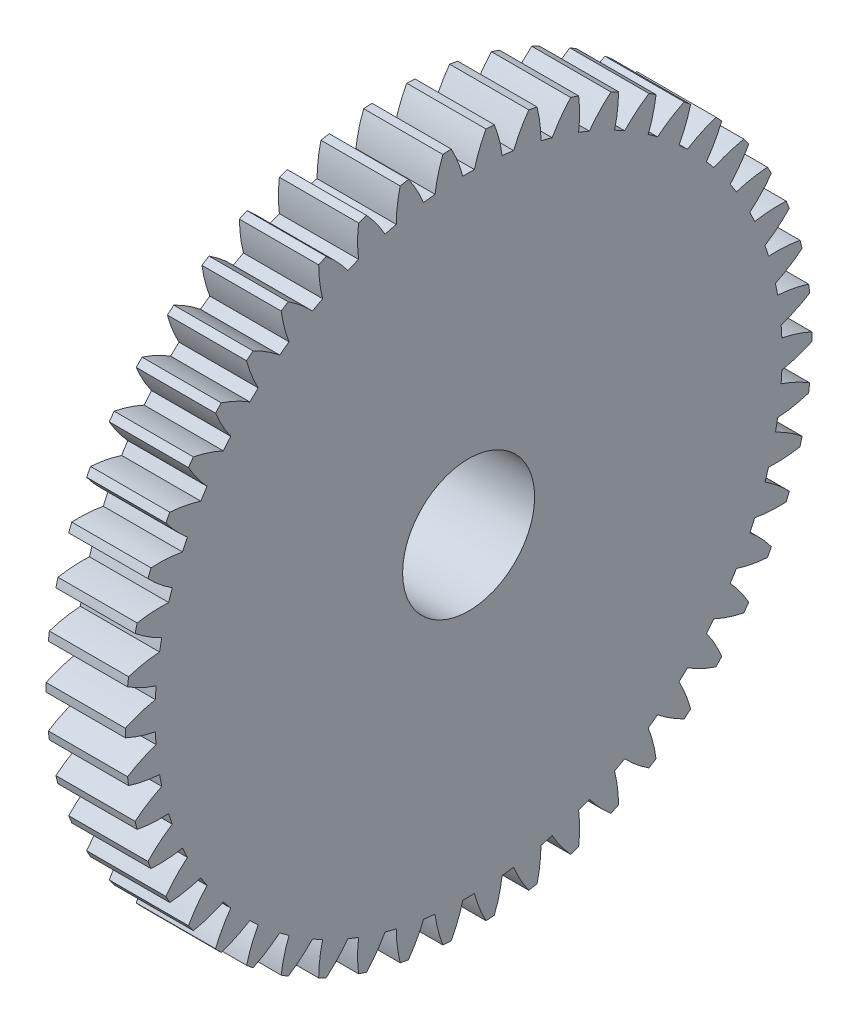
SolidWorks part; units mm, degrees
material "铬红铜，UNS C18200"
ref_plane "Plane1" through (0, 0, 0) normal (0, 0, 1) x (1, 0, 0)
ref_plane "Plane2" through (0, 0, 0) normal (0, 1, 0) x (1, 0, 0)
ref_plane "Plane3" through (0, 0, 0) normal (1, 0, 0) x (0, 0, -1)
sketch "HoldingSke" plane through (0, 0, 0) normal (0, 1, 0) x (1, 0, 0)
  line L0 (0, 0) -> (1.2856, -1.5321)
  line L1 (-15, 0) -> (100, 0) construction
  line L2 (0, 0) -> (-2.1039, 2.3779)
  line L3 (0, 0) -> (-11.863, 4.5341)
  line L4 (0, 0) -> (5.5511, 6.6156)
  line L5 (0, 0) -> (-7.4956, -2.7956)
  line L6 (0, 0) -> (-2.4869, -1.6779)
  line L7 (-2.1039, 2.3779) -> (-0.3819, 10.1904)
  line L8 (-76.2, 54.61) -> (-75.3, 54.61)
  line L9 (-71.009, 38.7566) -> (-53.1078, 45.2721)
  line L10 (-76.2, 71.12) -> (104.1128, 71.12)
  line L11 (0, 0) -> (-3, 0)
  line L12 (-76.2, 101.6) -> (-76.181, 101.6)
  line L13 (24.9733, 27.94) -> (52.9518, 28.4284)
  line L14 (24.9733, 27.94) -> (24.9743, 27.94)
  line L15 (24.9733, 27.94) -> (100.4006, 29.5858)
  line L16 (-63.627, -0.5) -> (-12.827, -0.5)
  circle A0 centre (0, 0) radius 2.5
  circle A1 centre (0, 0) radius 4.5
  circle A2 centre (0, 0) radius 4.5
  circle A3 centre (0, 0) radius 2.5
  dimension "MHD" = 9
  dimension "Hub_dia" = 9
  dimension "Bore" = 5
  dimension "MBD" = 5
  dimension "Num_teeth" = 50
  dimension "Pitch_radius" = 180.3128
  dimension "Pitch" = 2
  dimension "Width" = 3
  dimension "Overall_len" = 8
  dimension "Show_teeth" = 50
  dimension "Thickness" = 3
  dimension "OAL" = 8.0001
  dimension "T_dim" = 0.9
  dimension "Ap" = 20
  dimension "H" = 19.05
  dimension "Backlash" = 0.019
  dimension "Addendum_fac" = 1
  dimension "Dedendum_fac" = 1.25
  dimension "Clearance_fac" = 0.25
  dimension "Dedendum_add" = 0.001
  dimension "Module" = 0.5
sketch "BasProSke" plane through (0, 0, 0) normal (0, 1, 0) x (1, 0, 0)
  line L0 (-10, 0) -> (60, 0) construction
  line L1 (0, 0) -> (0, 13)
  line L2 (0, 0) -> (3, 0)
  line L3 (3, 0) -> (3, 13)
  line L4 (3, 13) -> (0, 13)
  dimension "Diameter" = 26
  dimension "Thickness" = 3
revolve "Base-Revolve" add sketch "BasProSke" angle 360 about L0
sketch "TooCutSke" plane through (0, 0, 0) normal (1, 0, 0) x (0, 0, -1)
  line L1 (0, 0) -> (0, 107) construction
  line L2 (0, 0) -> (-0.4259, 12.4927) construction
  line L3 (0, 0) -> (-1.5691, 24.9404) construction
  line L4 (-0.4259, 12.4927) -> (-0.7846, 12.4702) construction
  arc A0 (0.2187, 11.872) -> (-0.2187, 11.872) centre (0, 0) ccw
  arc A1 (0.6715, 13.0081) -> (-0.6715, 13.0081) centre (0, 0) ccw
  circle A2 centre (0, 0) radius 12.5 construction
  circle A3 centre (0, 0) radius 11.7462 construction
  arc A4 (-0.2187, 11.872) -> (-0.6715, 13.0081) centre (-5.0549, 10.6028) ccw
  arc A5 (0.6715, 13.0081) -> (0.2187, 11.872) centre (5.0549, 10.6028) ccw
  dimension "Root_dia" = 23.748
  dimension "Overcut_dia" = 26.0508
  dimension "Pitch_dia" = 25
  dimension "Base_dia" = 23.4923
  dimension "Flank_rad" = 5
  dimension "Half_ang" = 3.6
  dimension "Half_CT" = 0.3594
extrude "ToothCut" cut sketch "TooCutSke" along normal through all
fillet "Breaks" [suppressed] radius 0.01
fillet "RootFillets" [suppressed] radius 0.126
pattern_circular "TeethCuts" count 50 every 7.2 about axis through (-10, 0, 0) along (1, 0, 0) of "ToothCut", "RootFillets", "Breaks"
sketch "HubNeaOneSke" plane through (0, 0, 0) normal (-1, 0, 0) x (0, 0, 1)
  circle A0 centre (0, 0) radius 4.5
  dimension "Diameter" = 9
extrude "HubNearOne" add sketch "HubNeaOneSke" along normal blind 5.0001
sketch "HubNeaBotSke" plane through (0, 0, 0) normal (-1, 0, 0) x (0, 0, 1)
  circle A0 centre (0, 0) radius 4.5
  dimension "Diameter" = 9
extrude "HubNearBoth" [suppressed] add sketch "HubNeaBotSke" along normal blind 2.5
ref_plane "FarPln" through (3, 0, 0) normal (1, 0, 0) x (0, 0, -1)
sketch "HubFarSke" plane through (3, 0, 0) normal (1, 0, 0) x (0, 0, -1)
  circle A0 centre (0, 0) radius 4.5
  dimension "Diameter" = 9
extrude "HubFar" [suppressed] add sketch "HubFarSke" along normal blind 2.5
sketch "BorSke" plane through (0, 0, 0) normal (1, 0, 0) x (0, 0, -1)
  circle A0 centre (0, 0) radius 2.5
  dimension "Diameter" = 5
extrude "Bore" cut sketch "BorSke" along normal mid plane 16.0001
sketch "KeySke" plane through (0, 0, 0) normal (1, 0, 0) x (0, 0, -1)
  line L0 (-1, 0) -> (-1, 3.4)
  line L1 (-1, 3.4) -> (1, 3.4)
  line L2 (1, 3.4) -> (1, 0)
  line L3 (0, 0) -> (0, 34) construction
  line L4 (-1, 0) -> (1, 0)
  dimension "Offset" = 3.4
  dimension "Width" = 2
extrude "Keyway" [suppressed] cut sketch "KeySke" along normal mid plane 16.0001
pattern_circular "Keyway2" [suppressed] count 2 every 90 about axis through (-10, 0, 0) along (1, 0, 0)
equation "' \"Module@HoldingSke\" = 6.35"
equation "' \"Num_teeth@HoldingSke\" = 12"
equation "' \"Ap@HoldingSke\" =  20"
equation "' \"Width@HoldingSke\" = 0.5 * 25.4"
equation "' \"Hub_dia@HoldingSke\"= 1 * 25.4"
equation "' \"Overall_len@HoldingSke\" = 1.0 * 25.4"
equation "' \"Bore@HoldingSke\" = 0.75 * 25.4"
equation "' \"T_dim@HoldingSke\" = 0.1 * 25.4"
equation "' \"Width@KeySke\" = 0.25 * 25.4"
equation "' \"Show_teeth@HoldingSke\" = 13"
equation "' \"Backlash@HoldingSke\" = 0.009 * 25.4"
equation "' \"Addendum_fac@HoldingSke\" = 1.0"
equation "' \"Dedendum_fac@HoldingSke\" = 1.25"
equation "' \"Dedendum_add@HoldingSke\" = 0.00005 * 25.4"
equation "' \"Clearance_fac@HoldingSke\" = 0.25"
equation "\"Pitch@HoldingSke\" = 1 / \"Module@HoldingSke\""
equation "\"Overcut_dia@TooCutSke\" = (\"Num_teeth@HoldingSke\" + 2 * \"Addendum_fac@HoldingSke\") / \"Pitch@HoldingSke\" + 0.002 * 25.4"
equation "\"Pitch_dia@TooCutSke\" = \"Num_teeth@HoldingSke\" / \"Pitch@HoldingSke\""
equation "\"Base_dia@TooCutSke\" = \"Num_teeth@HoldingSke\" / \"Pitch@HoldingSke\" * cos((\"Ap@HoldingSke\"  * 3.14159265 / 180))"
equation "\"Root_dia@TooCutSke\" = (\"Num_teeth@HoldingSke\" + 2) / \"Pitch@HoldingSke\" - 2 * (\"Addendum_fac@HoldingSke\" + \"Dedendum_fac@HoldingSke\") / \"Pitch@HoldingSke\" - \"Dedendum_add@HoldingSke\" * 2"
equation "\"Half_ang@TooCutSke\" = 180 / \"Num_teeth@HoldingSke\""
equation "\"Half_CT@TooCutSke\" = \"Num_teeth@HoldingSke\" / \"Pitch@HoldingSke\" * sin((3.14159265 / 2 / \"Num_teeth@HoldingSke\")) / 2 - 7 * \"Backlash@HoldingSke\" / 4"
equation "\"Flank_rad@TooCutSke\" = \"Num_teeth@HoldingSke\" / \"Pitch@HoldingSke\" / 5"
equation "\"Radius@RootFillets\" = \"Clearance_fac@HoldingSke\" / \"Pitch@HoldingSke\" + \"Dedendum_add@HoldingSke\""
equation "\"Break_rad@Breaks\" = 0.02 / \"Pitch@HoldingSke\""
equation "\"Thickness@HoldingSke\" = \"Width@HoldingSke\""
equation "\"OAL@HoldingSke\" = \"Thickness@HoldingSke\""
equation "\"MHD@HoldingSke\" = (\"Num_teeth@HoldingSke\" + 2) / \"Pitch@HoldingSke\" - 2 * (\"Addendum_fac@HoldingSke\" + \"Dedendum_fac@HoldingSke\")  / \"Pitch@HoldingSke\" - \"Dedendum_add@HoldingSke\" * 2"
equation "\"MBD@HoldingSke\" = (\"Num_teeth@HoldingSke\" + 2) / \"Pitch@HoldingSke\" - 2 * (\"Addendum_fac@HoldingSke\" + \"Dedendum_fac@HoldingSke\")  / \"Pitch@HoldingSke\" - \"Dedendum_add@HoldingSke\" * 2 - 0.002 * 25.4"
equation "\"MHD@HoldingSke\" = ((sgn( \"MHD@HoldingSke\" - \"Hub_dia@HoldingSke\" )-1)*( \"MHD@HoldingSke\" - \"Hub_dia@HoldingSke\" ))/-2+ \"Hub_dia@HoldingSke\""
equation "\"MBD@HoldingSke\" = ((sgn( \"MBD@HoldingSke\" - \"Bore@HoldingSke\" )-1)*( \"MBD@HoldingSke\" - \"Bore@HoldingSke\" ))/-2+ \"Bore@HoldingSke\""
equation "\"OAL@HoldingSke\" = ((sgn( \"OAL@HoldingSke\" - \"Overall_len@HoldingSke\" )+1)*( \"OAL@HoldingSke\" - \"Overall_len@HoldingSke\" ))/2 + \"Overall_len@HoldingSke\" + 0.000002 * 25.4"
equation "\"Num_teeth@TeethCuts\" = int( \"Show_teeth@HoldingSke\" ) + 1"
equation "\"Num_teeth@TeethCuts\" = ((sgn( \"Num_teeth@TeethCuts\" - \"Num_teeth@HoldingSke\" )-1)*( \"Num_teeth@TeethCuts\" - \"Num_teeth@HoldingSke\" ))/-2+ \"Num_teeth@HoldingSke\""
equation "\"Num_teeth@TeethCuts\" = ((sgn( \"Num_teeth@TeethCuts\" - 2.0)+1)*( \"Num_teeth@TeethCuts\" - 2.0))/2 +2.0"
equation "\"Angle@TeethCuts\" = 360.0 / \"Num_teeth@HoldingSke\""
equation "\"Diameter@BasProSke\" = (\"Num_teeth@HoldingSke\" + 2 * \"Addendum_fac@HoldingSke\") / \"Pitch@HoldingSke\""
equation "\"Thickness@BasProSke\"  = \"Thickness@HoldingSke\""
equation "' \"Fillet_rad@BasProSke\" =  \"Thickness@HoldingSke\" * 0.05"
equation "\"MHD@HoldingSke\" = ((sgn( \"MHD@HoldingSke\" - \"Root_dia@TooCutSke\" )-1)*( \"MHD@HoldingSke\" - \"Root_dia@TooCutSke\" ))/-2+ \"Root_dia@TooCutSke\""
equation "\"Diameter@HubNeaOneSke\" = \"MHD@HoldingSke\""
equation "\"Length@HubNearOne\" = \"OAL@HoldingSke\" - \"Thickness@BasProSke\""
equation "\"Diameter@HubNeaBotSke\" = \"MHD@HoldingSke\""
equation "\"Length@HubNearBoth\" = ( \"OAL@HoldingSke\" - \"Thickness@BasProSke\" ) / 2.0"
equation "\"Thickness@FarPln\" = \"Thickness@BasProSke\""
equation "\"Diameter@HubFarSke\" = \"MHD@HoldingSke\""
equation "\"Length@HubFar\" = ( \"OAL@HoldingSke\" - \"Thickness@BasProSke\" ) / 2.0"
equation "\"Diameter@BorSke\" = \"MBD@HoldingSke\""
equation "\"D1@Bore\" = \"OAL@HoldingSke\" * 2.0"
equation "\"D1@Keyway\" = \"OAL@HoldingSke\" * 2.0"
equation "\"Offset@KeySke\" = \"T_dim@HoldingSke\" + \"MBD@HoldingSke\" / 2.0"
